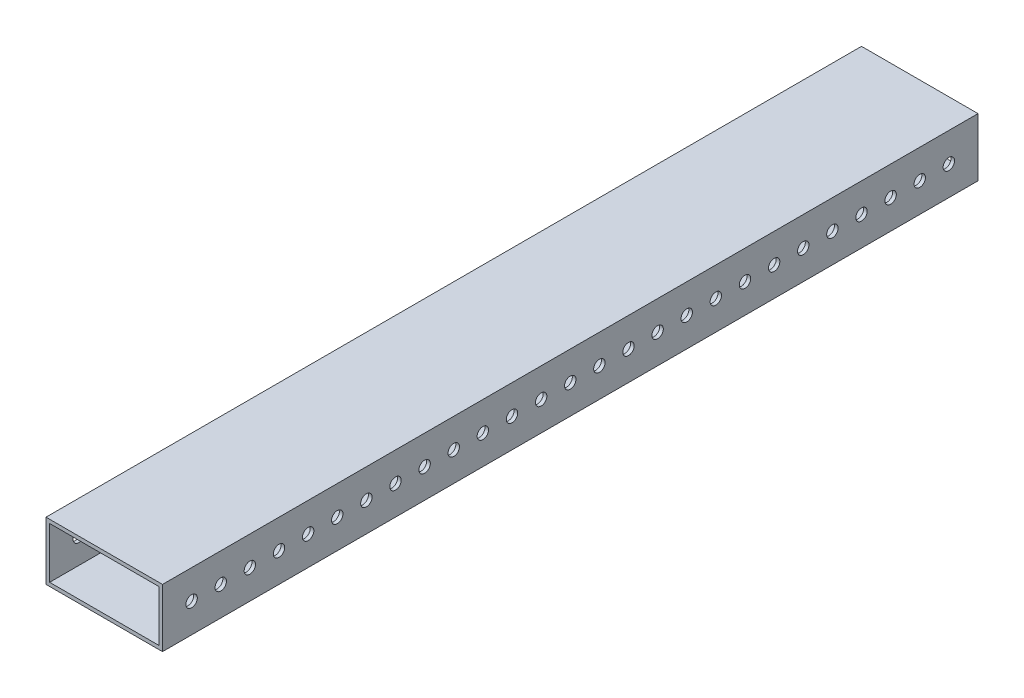
SolidWorks part; units mm, degrees
material "6061 Alloy"
ref_plane "Front Plane" through (0, 0, 0) normal (0, 0, 1) x (1, 0, 0)
ref_plane "Top Plane" through (0, 0, 0) normal (0, 1, 0) x (1, 0, 0)
ref_plane "Right Plane" through (0, 0, 0) normal (1, 0, 0) x (0, 0, -1)
sketch "Sketch1" plane through (0, 0, 0) normal (0, 0, 1) x (1, 0, 0)
  line L0 (1.5875, 1.5875) -> (49.2125, 1.5875)
  line L1 (0, 0) -> (50.8, 0)
  line L2 (0, 0) -> (0, 25.4)
  line L3 (0, 25.4) -> (50.8, 25.4)
  line L4 (50.8, 0) -> (50.8, 25.4)
  line L5 (49.2125, 1.5875) -> (49.2125, 23.8125)
  line L6 (1.5875, 23.8125) -> (49.2125, 23.8125)
  line L7 (1.5875, 1.5875) -> (1.5875, 23.8125)
  dimension "D1" = 50.8
  dimension "D2" = 25.4
  dimension "D3" = 1.5875
extrude "Boss-Extrude1" add sketch "Sketch1" along normal blind 355.6
sketch "Sketch2" plane through (50.8, 0, 0) normal (1, 0, 0) x (0, 0, -1)
  line L0 (-355.6, 0) -> (-355.6, 25.4) construction
  line L1 (-342.9, 12.7) -> (-330.2, 12.7) construction
  circle A0 centre (-342.9, 12.7) radius 2.4892
  circle A1 centre (-330.2, 12.7) radius 2.4892
  circle A2 centre (-317.5, 12.7) radius 2.4892
  circle A3 centre (-304.8, 12.7) radius 2.4892
  circle A4 centre (-292.1, 12.7) radius 2.4892
  circle A5 centre (-279.4, 12.7) radius 2.4892
  circle A6 centre (-266.7, 12.7) radius 2.4892
  circle A7 centre (-254, 12.7) radius 2.4892
  circle A8 centre (-241.3, 12.7) radius 2.4892
  circle A9 centre (-228.6, 12.7) radius 2.4892
  circle A10 centre (-215.9, 12.7) radius 2.4892
  circle A11 centre (-203.2, 12.7) radius 2.4892
  circle A12 centre (-190.5, 12.7) radius 2.4892
  circle A13 centre (-177.8, 12.7) radius 2.4892
  circle A14 centre (-165.1, 12.7) radius 2.4892
  circle A15 centre (-152.4, 12.7) radius 2.4892
  circle A16 centre (-139.7, 12.7) radius 2.4892
  circle A17 centre (-127, 12.7) radius 2.4892
  circle A18 centre (-114.3, 12.7) radius 2.4892
  circle A19 centre (-101.6, 12.7) radius 2.4892
  circle A20 centre (-88.9, 12.7) radius 2.4892
  circle A21 centre (-76.2, 12.7) radius 2.4892
  circle A22 centre (-63.5, 12.7) radius 2.4892
  circle A23 centre (-50.8, 12.7) radius 2.4892
  circle A24 centre (-38.1, 12.7) radius 2.4892
  circle A25 centre (-25.4, 12.7) radius 2.4892
  circle A26 centre (-12.7, 12.7) radius 2.4892
  point P4 (-355.6, 12.7)
  dimension "D1" = 4.9784
  dimension "D2" = 12.7
  dimension "D4" = 12.7
  dimension "D3" = 27
extrude "Cut-Extrude1" cut sketch "Sketch2" against normal through all
